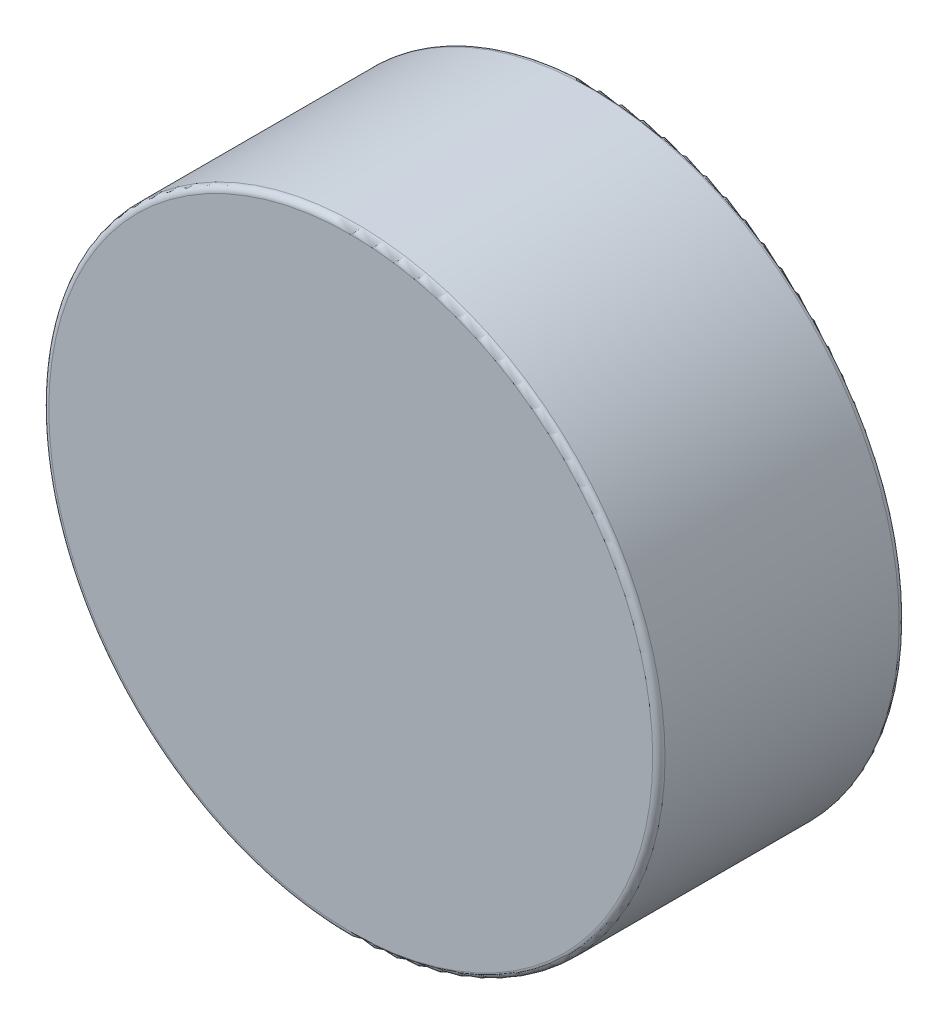
SolidWorks part; units mm, degrees
ref_plane "Front Plane" through (0, 0, 0) normal (0, 0, 1) x (1, 0, 0)
ref_plane "Top Plane" through (0, 0, 0) normal (0, 1, 0) x (1, 0, 0)
ref_plane "Right Plane" through (0, 0, 0) normal (1, 0, 0) x (0, 0, -1)
sketch "Sketch1" plane through (0, 0, 0) normal (0, 0, 1) x (1, 0, 0)
  circle A0 centre (0, 0) radius 3.175 construction
  dimension "OD" = 6.35
sketch "Sketch2" plane through (0, 0, 0) normal (1, 0, 0) x (0, 0, -1)
  line L0 (-1.27, 0) -> (1.27, 0) construction
  line L1 (0, 3.175) -> (0, -3.175) construction
  line L3 (-1.27, 3.175) -> (1.27, 3.175)
  line L4 (-1.27, 3.175) -> (-1.27, -3.175)
  line L5 (-1.27, -3.175) -> (1.27, -3.175)
  line L6 (1.27, 3.175) -> (1.27, -3.175)
  point P4 (0, 0)
  point P12 (0, 3.175)
  dimension "Thickness" = 2.54
sketch "Sketch3" plane through (0, 0, 0) normal (0, 0, 1) x (1, 0, 0)
  circle A0 centre (0, 0) radius 3.175 construction
  circle A1 centre (0, 0) radius 3.175
extrude "Boss-Extrude1" add sketch "Sketch3" along normal up to vertex (1.27 mm away) and the other way up to vertex (1.27 mm away) up to point (0, 3.175, 1.27) other way up to point (0, 3.175, -1.27)
fillet "Fillet1" radius 0.0635 2 edges at (3.175, 0, -1.27) (3.175, 0, 1.27)
equation "\"Fillet@Fillet1\"=\"Thickness@Sketch2\"*.025"
